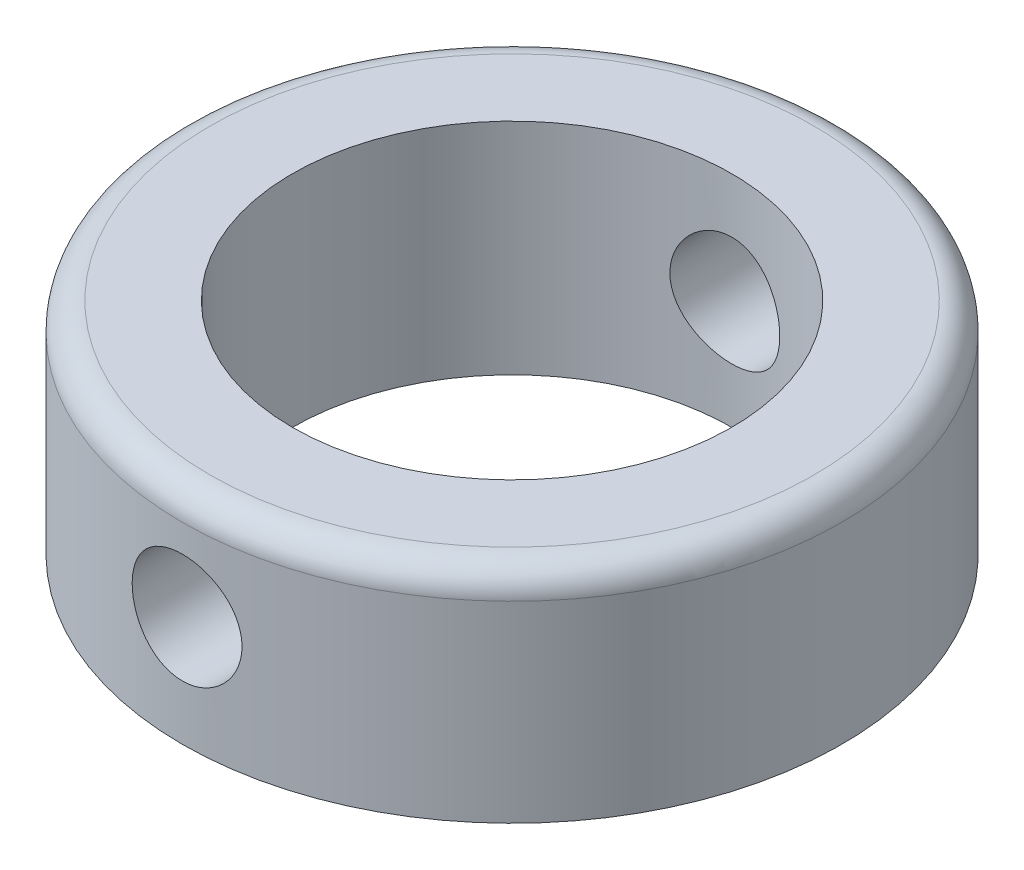
SolidWorks part; units mm, degrees
ref_plane "Front Plane" through (0, 0, 0) normal (0, 0, 1) x (1, 0, 0)
ref_plane "Top Plane" through (0, 0, 0) normal (0, 1, 0) x (1, 0, 0)
ref_plane "Right Plane" through (0, 0, 0) normal (1, 0, 0) x (0, 0, -1)
sketch "Sketch1" plane through (0, 0, 0) normal (0, 1, 0) x (1, 0, 0)
  circle A0 centre (0, 0) radius 8
  circle A1 centre (0, 0) radius 12
  dimension "D1" = 16
  dimension "D2" = 24
extrude "Boss-Extrude1" add sketch "Sketch1" along normal mid plane 8
fillet "Fillet1" radius 1 1 edges at (0, 4, 12)
sketch "Sketch2" plane through (0, 0, 0) normal (0, 0, 1) x (1, 0, 0)
  circle A0 centre (0, 0) radius 2
  dimension "D1" = 4
extrude "Cut-Extrude1" cut sketch "Sketch2" against normal mid plane 50
